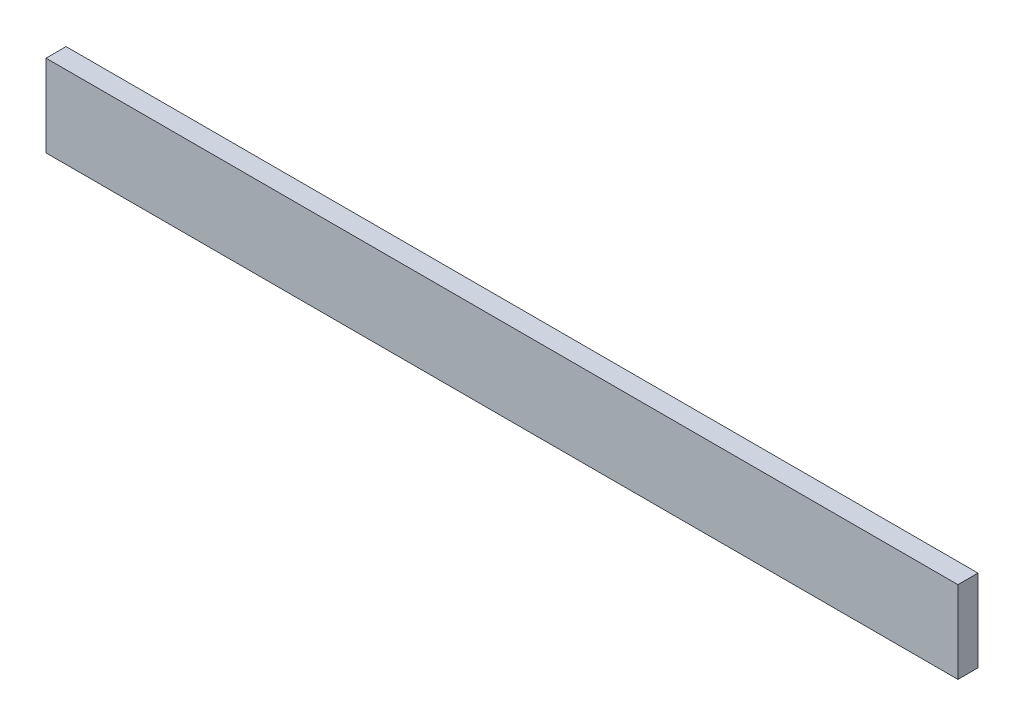
SolidWorks part; units mm, degrees
ref_plane "Face" through (0, 0, 0) normal (0, 0, 1) x (1, 0, 0)
ref_plane "Dessus" through (0, 0, 0) normal (0, 1, 0) x (1, 0, 0)
ref_plane "Droite" through (0, 0, 0) normal (1, 0, 0) x (0, 0, -1)
sketch "Esquisse1" plane through (0, 0, 0) normal (0, 0, 1) x (1, 0, 0)
  line L1 (0, 0) -> (1000, 0)
  line L2 (0, 0) -> (0, 90)
  line L3 (0, 90) -> (1000, 90)
  line L4 (1000, 0) -> (1000, 90)
  dimension "D1" = 1000
  dimension "D2" = 90
extrude "Extrusion1" add sketch "Esquisse1" along normal blind 22
